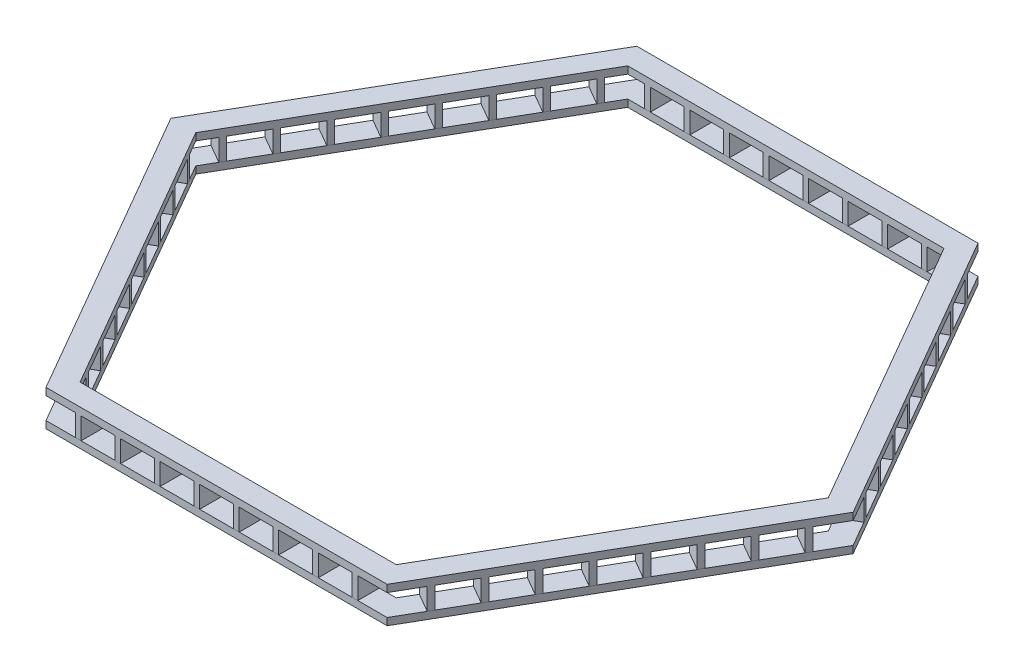
SolidWorks part; units mm, degrees
ref_plane "前视基准面" through (0, 0, 0) normal (0, 0, 1) x (1, 0, 0)
ref_plane "上视基准面" through (0, 0, 0) normal (0, 1, 0) x (1, 0, 0)
ref_plane "右视基准面" through (0, 0, 0) normal (1, 0, 0) x (0, 0, -1)
sketch "草图1" plane through (0, 0, 0) normal (0, 1, 0) x (1, 0, 0)
  line L0 (-1186.6025, -2055.2559) -> (1186.6025, -2055.2559)
  line L1 (-1100, -1905.2559) -> (1100, -1905.2559)
  line L2 (1100, -1905.2559) -> (2200, 0)
  line L3 (2200, 0) -> (1100, 1905.2559)
  line L4 (1100, 1905.2559) -> (-1100, 1905.2559)
  line L5 (-1100, 1905.2559) -> (-2200, 0)
  line L6 (-2200, 0) -> (-1100, -1905.2559)
  line L7 (1186.6025, -2055.2559) -> (2373.2051, 0)
  line L8 (2373.2051, 0) -> (1186.6025, 2055.2559)
  line L9 (1186.6025, 2055.2559) -> (-1186.6025, 2055.2559)
  line L10 (-1186.6025, 2055.2559) -> (-2373.2051, 0)
  line L11 (-2373.2051, 0) -> (-1186.6025, -2055.2559)
  circle A0 centre (0, 0) radius 1905.2559 construction
  dimension "D1" = 2200
  dimension "D2" = 150
extrude "凸台-拉伸2" add sketch "草图1" along normal blind 50
ref_plane "基准面2" through (0, 50, 0) normal (0, 1, 0) x (1, 0, 0)
sketch "草图2" plane through (0, 50, 0) normal (0, 1, 0) x (1, 0, 0)
  line L0 (0, 1905.2559) -> (0, 2055.2559) construction
  line L1 (1100, 1905.2559) -> (-1100, 1905.2559) construction
  line L2 (1186.6025, 2055.2559) -> (-1186.6025, 2055.2559) construction
  line L3 (-1100, 1905.2559) -> (-1100, 2055.2559) construction
  line L4 (1100, 1905.2559) -> (1100, 2055.2559) construction
  line L5 (0, 1905.2559) -> (-1100, 1905.2559) construction
  line L6 (-550, 1905.2559) -> (-550, 2055.2559) construction
  line L7 (-550, 2055.2559) -> (0, 2055.2559) construction
  line L8 (0, 1905.2559) -> (1100, 1905.2559) construction
  line L9 (550, 1905.2559) -> (550, 2055.2559) construction
  line L10 (0, 2055.2559) -> (550, 2055.2559) construction
  line L11 (550, 2055.2559) -> (1100, 2055.2559) construction
  line L12 (275, 2055.2559) -> (275, 1905.2559) construction
  line L13 (825, 2055.2559) -> (825, 1905.2559) construction
  line L14 (0, 2055.2559) -> (-550, 2055.2559) construction
  line L15 (-550, 2055.2559) -> (-1100, 2055.2559) construction
  line L16 (-825, 2055.2559) -> (-825, 1905.2559) construction
  line L17 (-275, 2055.2559) -> (-275, 1905.2559) construction
  line L18 (275, 2055.2559) -> (0, 2055.2559) construction
  line L19 (137.5, 2055.2559) -> (137.5, 1905.2559) construction
  line L20 (275, 2055.2559) -> (550, 2055.2559) construction
  line L21 (550, 2055.2559) -> (825, 2055.2559) construction
  line L22 (825, 2055.2559) -> (1100, 2055.2559) construction
  line L23 (412.5, 2055.2559) -> (412.5, 1905.2559) construction
  line L24 (687.5, 2055.2559) -> (687.5, 1905.2559) construction
  line L25 (962.5, 2055.2559) -> (962.5, 1905.2559) construction
  line L26 (0, 2055.2559) -> (-275, 2055.2559) construction
  line L27 (-275, 2055.2559) -> (-550, 2055.2559) construction
  line L28 (-550, 2055.2559) -> (-825, 2055.2559) construction
  line L29 (-825, 2055.2559) -> (-1100, 2055.2559) construction
  line L30 (-962.5, 2055.2559) -> (-962.5, 1905.2559) construction
  line L31 (-687.5, 2055.2559) -> (-687.5, 1905.2559) construction
  line L32 (-412.5, 2055.2559) -> (-412.5, 1905.2559) construction
  line L33 (-137.5, 2055.2559) -> (-137.5, 1905.2559) construction
  line L34 (117.5, 1905.2559) -> (117.5, 2055.2559)
  line L35 (117.5, 1905.2559) -> (157.5, 1905.2559)
  line L36 (117.5, 2055.2559) -> (157.5, 2055.2559)
  line L37 (157.5, 1905.2559) -> (157.5, 2055.2559)
  line L38 (117.5, 1905.2559) -> (157.5, 2055.2559) construction
  line L39 (117.5, 2055.2559) -> (157.5, 1905.2559) construction
  line L40 (432.5, 2055.2559) -> (392.5, 1905.2559) construction
  line L41 (432.5, 1905.2559) -> (392.5, 2055.2559) construction
  line L42 (432.5, 1905.2559) -> (392.5, 1905.2559)
  line L43 (432.5, 1905.2559) -> (432.5, 2055.2559)
  line L44 (432.5, 2055.2559) -> (392.5, 2055.2559)
  line L45 (392.5, 1905.2559) -> (392.5, 2055.2559)
  line L46 (667.5, 1905.2559) -> (707.5, 1905.2559)
  line L47 (667.5, 1905.2559) -> (707.5, 2055.2559) construction
  line L48 (667.5, 2055.2559) -> (707.5, 1905.2559) construction
  line L49 (667.5, 1905.2559) -> (667.5, 2055.2559)
  line L50 (707.5, 1905.2559) -> (707.5, 2055.2559)
  line L51 (667.5, 2055.2559) -> (707.5, 2055.2559)
  line L52 (982.5, 1905.2559) -> (942.5, 2055.2559) construction
  line L53 (982.5, 2055.2559) -> (942.5, 1905.2559) construction
  line L54 (982.5, 1905.2559) -> (942.5, 1905.2559)
  line L55 (982.5, 1905.2559) -> (982.5, 2055.2559)
  line L56 (982.5, 2055.2559) -> (942.5, 2055.2559)
  line L57 (942.5, 1905.2559) -> (942.5, 2055.2559)
  line L58 (-432.5, 1905.2559) -> (-432.5, 2055.2559)
  line L59 (-982.5, 2055.2559) -> (-942.5, 2055.2559)
  line L60 (-982.5, 1905.2559) -> (-942.5, 1905.2559)
  line L61 (-942.5, 1905.2559) -> (-942.5, 2055.2559)
  line L62 (-982.5, 1905.2559) -> (-982.5, 2055.2559)
  line L63 (-667.5, 1905.2559) -> (-707.5, 1905.2559)
  line L64 (-707.5, 1905.2559) -> (-707.5, 2055.2559)
  line L65 (-667.5, 2055.2559) -> (-707.5, 2055.2559)
  line L66 (-667.5, 1905.2559) -> (-667.5, 2055.2559)
  line L67 (-432.5, 1905.2559) -> (-392.5, 1905.2559)
  line L68 (-432.5, 2055.2559) -> (-392.5, 2055.2559)
  line L69 (-392.5, 1905.2559) -> (-392.5, 2055.2559)
  line L70 (-117.5, 1905.2559) -> (-157.5, 1905.2559)
  line L71 (-117.5, 1905.2559) -> (-117.5, 2055.2559)
  line L72 (-117.5, 2055.2559) -> (-157.5, 2055.2559)
  line L73 (-157.5, 1905.2559) -> (-157.5, 2055.2559)
  point P40 (137.5, 1973.2927)
  point P41 (137.5, 1980.2559)
  point P42 (123.3846, 1976.495)
  point P47 (137.5, 1980.2559)
  point P76 (0, 0)
  dimension "D1" = 40
extrude "凸台-拉伸3" add sketch "草图2" along normal blind 150 separate body
sketch "草图3" plane through (0, 0, 0) normal (0, 0, 1) x (1, 0, 0)
  line L0 (0, 0) -> (0, 600) construction
  dimension "D1" = 600
pattern_circular "阵列(圆周)2" count 6 every 60 about axis through (0, 0, 0) along (0, 1, 0) of bodies 171 169 173 174 172 108 168 170
ref_plane "基准面3" through (0, 200, 0) normal (0, 1, 0) x (1, 0, 0)
sketch "草图5" plane through (0, 200, 0) normal (0, 1, 0) x (1, 0, 0)
  line L0 (-2373.2051, 0) -> (-1186.6025, -2055.2559) construction
  line L1 (-2200, 0) -> (-1100, -1905.2559) construction
  line L2 (-1186.6025, -2055.2559) -> (1186.6025, -2055.2559) construction
  line L3 (-1100, -1905.2559) -> (1100, -1905.2559) construction
  line L4 (1100, -1905.2559) -> (2200, 0) construction
  line L5 (1186.6025, -2055.2559) -> (2373.2051, 0) construction
  line L6 (2373.2051, 0) -> (1186.6025, 2055.2559) construction
  line L7 (2200, 0) -> (1100, 1905.2559) construction
  line L8 (1100, 1905.2559) -> (-1100, 1905.2559) construction
  line L9 (1186.6025, 2055.2559) -> (-1186.6025, 2055.2559) construction
  line L10 (-1186.6025, 2055.2559) -> (-2373.2051, 0) construction
  line L11 (-1100, 1905.2559) -> (-2200, 0) construction
  line L12 (-2373.2051, 0) -> (-1186.6025, -2055.2559)
  line L13 (-2200, 0) -> (-1100, -1905.2559)
  line L14 (-1186.6025, -2055.2559) -> (1186.6025, -2055.2559)
  line L15 (-1100, -1905.2559) -> (1100, -1905.2559)
  line L16 (1100, -1905.2559) -> (2200, 0)
  line L17 (1186.6025, -2055.2559) -> (2373.2051, 0)
  line L18 (2373.2051, 0) -> (1186.6025, 2055.2559)
  line L19 (2200, 0) -> (1100, 1905.2559)
  line L20 (1100, 1905.2559) -> (-1100, 1905.2559)
  line L21 (1186.6025, 2055.2559) -> (-1186.6025, 2055.2559)
  line L22 (-1186.6025, 2055.2559) -> (-2373.2051, 0)
  line L23 (-1100, 1905.2559) -> (-2200, 0)
extrude "凸台-拉伸5" add sketch "草图5" along normal blind 50
